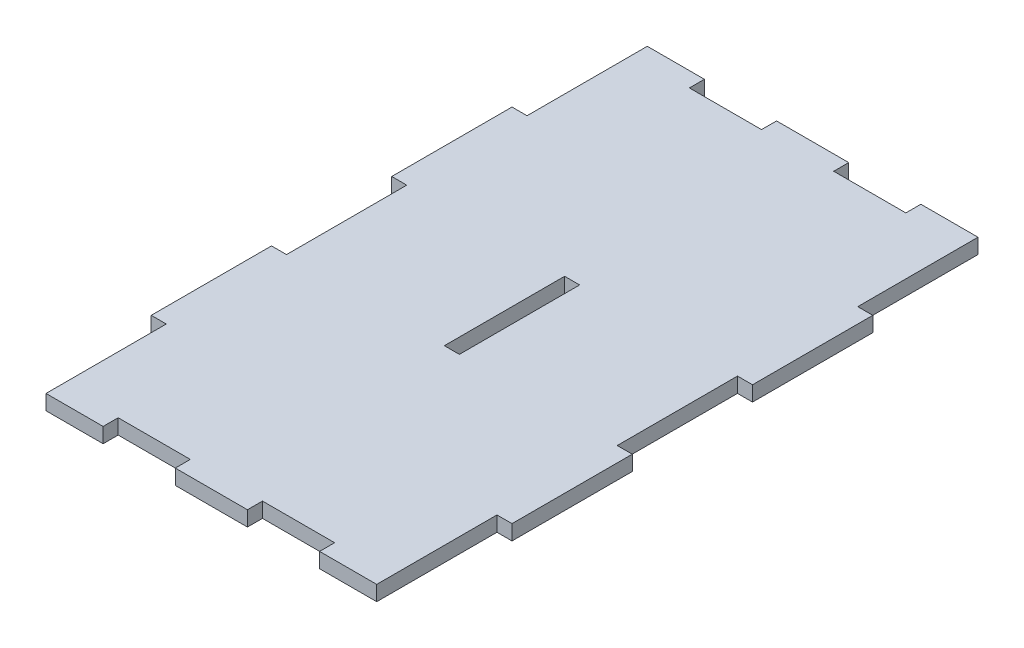
SolidWorks part; units mm, degrees
ref_plane "Front Plane" through (0, 0, 0) normal (0, 0, 1) x (1, 0, 0)
ref_plane "Top Plane" through (0, 0, 0) normal (0, 1, 0) x (1, 0, 0)
ref_plane "Right Plane" through (0, 0, 0) normal (1, 0, 0) x (0, 0, -1)
sketch "Sketch1" plane through (0, 0, 0) normal (0, 1, 0) x (1, 0, 0)
  line L1 (-38.1, -63.5) -> (38.1, -63.5)
  line L2 (-38.1, -63.5) -> (-38.1, 63.5)
  line L3 (-38.1, 63.5) -> (38.1, 63.5)
  line L4 (38.1, -63.5) -> (38.1, 63.5)
  line L5 (-38.1, -63.5) -> (38.1, 63.5) construction
  line L6 (-38.1, 63.5) -> (38.1, -63.5) construction
  point P0 (0, 0)
  dimension "D1" = 76.2
  dimension "D2" = 127
extrude "Boss-Extrude1" add sketch "Sketch1" along normal blind 3.175
sketch "Sketch2" plane through (0, 3.175, 0) normal (0, 1, 0) x (1, 0, 0)
  line L1 (-38.1, 63.5) -> (38.1, 63.5) construction
  line L2 (-38.1, 63.5) -> (-38.1, -63.5) construction
  line L3 (-38.1, -63.5) -> (38.1, -63.5) construction
  line L4 (38.1, 63.5) -> (38.1, -63.5) construction
  line L5 (-38.1, 63.5) -> (-34.925, 63.5)
  line L6 (-38.1, 63.5) -> (-38.1, 38.1)
  line L7 (-38.1, 38.1) -> (-34.925, 38.1)
  line L8 (-34.925, 63.5) -> (-34.925, 38.1)
  line L9 (38.1, 63.5) -> (34.925, 63.5)
  line L10 (38.1, 63.5) -> (38.1, 38.1)
  line L11 (38.1, 38.1) -> (34.925, 38.1)
  line L12 (34.925, 63.5) -> (34.925, 38.1)
  dimension "D1" = 3.175
  dimension "D2" = 25.4
  dimension "D3" = 25.4
  dimension "D4" = 3.175
extrude "Cut-Extrude1" cut sketch "Sketch2" against normal blind 3.175
pattern_linear "LPattern1" count 3 spacing 50.8 along (0, 0, 1) of "Cut-Extrude1"
sketch "Sketch3" plane through (0, 3.175, 0) normal (0, 1, 0) x (1, 0, 0)
  line L0 (-34.925, 63.5) -> (34.925, 63.5) construction
  line L1 (34.925, 63.5) -> (-34.925, 63.5) construction
  line L2 (-7.62, 63.5) -> (7.62, 63.5)
  line L3 (-7.62, 63.5) -> (-7.62, 60.325)
  line L4 (-7.62, 60.325) -> (7.62, 60.325)
  line L5 (7.62, 63.5) -> (7.62, 60.325)
  line L6 (-34.925, -63.5) -> (34.925, -63.5) construction
  line L7 (7.62, 63.5) -> (22.86, 63.5)
  line L8 (7.62, 63.5) -> (7.62, 60.325)
  line L9 (7.62, 60.325) -> (22.86, 60.325)
  line L10 (22.86, 63.5) -> (22.86, 60.325)
  line L11 (7.62, -63.5) -> (22.86, -63.5)
  line L12 (7.62, -63.5) -> (7.62, -60.325)
  line L13 (7.62, -60.325) -> (22.86, -60.325)
  line L14 (22.86, -63.5) -> (22.86, -60.325)
  line M15 (34.925, 63.5) -> (-34.925, 63.5)
  dimension "D1" = 69.85
  dimension "D2" = 15.24
  dimension "D3" = 3.175
  dimension "D4" = 27.305
  dimension "D5" = 15.24
  dimension "D6" = 3.175
extrude "Cut-Extrude2" cut sketch "Sketch3" against normal blind 3.175 contours L10 L5 L9 M15 | L13 L14 L11 L12
pattern_linear "LPattern2" count 3 spacing 30.48 along (-1, 0, 0) of "Cut-Extrude2"
sketch "Sketch4" plane through (0, 3.175, 0) normal (0, 1, 0) x (1, 0, 0)
  line L1 (-1.5875, 12.7) -> (1.5875, 12.7)
  line L2 (-1.5875, 12.7) -> (-1.5875, -12.7)
  line L3 (-1.5875, -12.7) -> (1.5875, -12.7)
  line L4 (1.5875, 12.7) -> (1.5875, -12.7)
  line L5 (-1.5875, 12.7) -> (1.5875, -12.7) construction
  line L6 (-1.5875, -12.7) -> (1.5875, 12.7) construction
  point P0 (0, 0)
  dimension "D1" = 25.4
  dimension "D2" = 3.175
extrude "Cut-Extrude3" cut sketch "Sketch4" against normal blind 3.175
